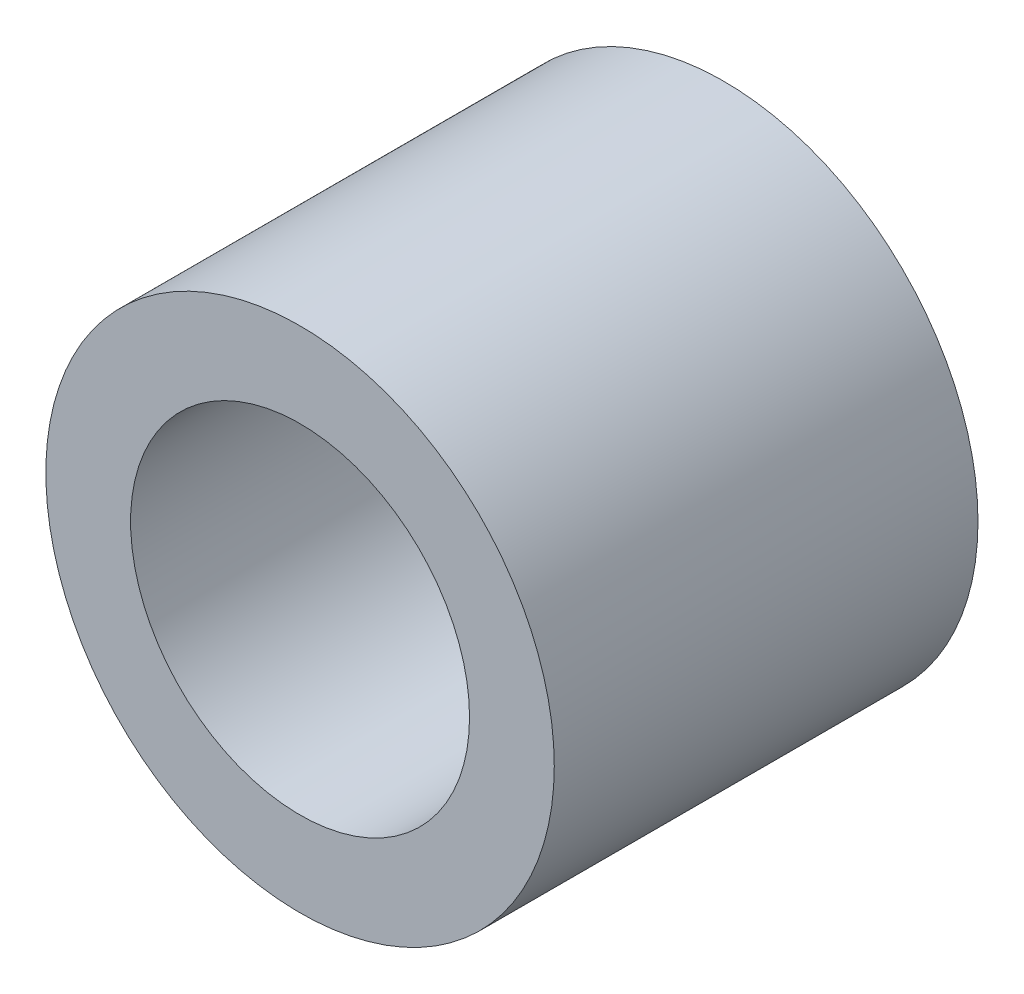
SolidWorks part; units mm, degrees
ref_plane "Front Plane" through (0, 0, 0) normal (0, 0, 1) x (1, 0, 0)
ref_plane "Top Plane" through (0, 0, 0) normal (0, 1, 0) x (1, 0, 0)
ref_plane "Right Plane" through (0, 0, 0) normal (1, 0, 0) x (0, 0, -1)
sketch "Sketch1" plane through (0, 0, 0) normal (0, 0, 1) x (1, 0, 0)
  line L0 (99.0537, 0) -> (-122.3936, 0) construction
  circle A0 centre (0, 0) radius 30
  circle A1 centre (0, 0) radius 20
  dimension "D1" = 60
  dimension "D2" = 40
extrude "Boss-Extrude2" add sketch "Sketch1" along normal mid plane 50
sketch "Sketch2" plane through (0, 0, 0) normal (0, 0, 1) x (1, 0, 0)
  line L0 (0, 0) -> (-123.0018, 0) construction
  line L1 (0, 0) -> (-110, 0)
  line L2 (-114.8303, 0) -> (-114.8303, 15)
  line L3 (-114.8303, 15) -> (-102.8303, 15)
  dimension "D1" = 110
  dimension "D2" = 15
  dimension "D3" = 12
